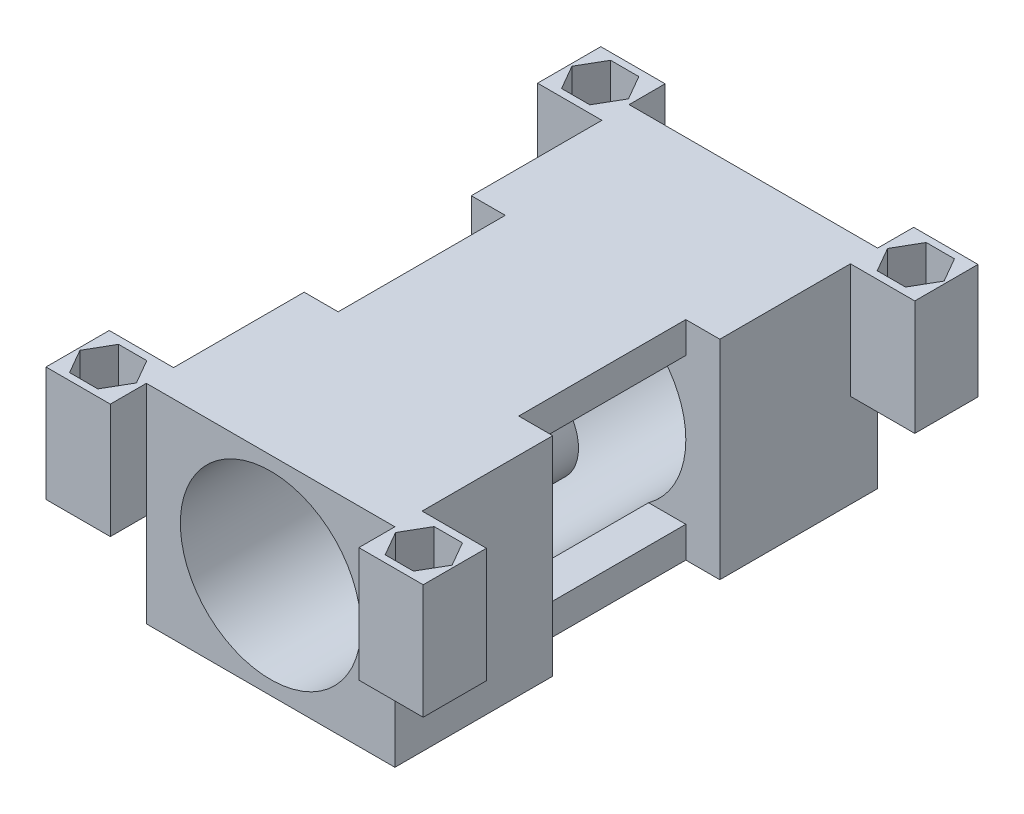
SolidWorks part; units mm, degrees
ref_plane "Front Plane" through (0, 0, 0) normal (0, 0, 1) x (1, 0, 0)
ref_plane "Top Plane" through (0, 0, 0) normal (0, 1, 0) x (1, 0, 0)
ref_plane "Right Plane" through (0, 0, 0) normal (1, 0, 0) x (0, 0, -1)
sketch "Sketch1" plane through (0, 0, 0) normal (0, 0, 1) x (1, 0, 0)
  line L0 (17, -14.25) -> (-17, -14.25)
  line L1 (-17, 14.25) -> (17, 14.25)
  line L2 (-17, 14.25) -> (-17, -14.25)
  line L3 (-17, 0) -> (17, 0) construction
  line L4 (17, 14.25) -> (17, -14.25)
  line L5 (0, 14.25) -> (0, -14.25) construction
  dimension "D2" = 34
  dimension "D3" = 28.5
extrude "Boss-Extrude1" add sketch "Sketch1" along normal blind 66.04
sketch "Sketch3" plane through (0, 0, 66.04) normal (0, 0, 1) x (1, 0, 0)
  circle A0 centre (0, 0) radius 12.35
  dimension "D1" = 24.7
extrude "Cut-Extrude1" cut sketch "Sketch3" against normal through all
sketch "Sketch7" plane through (0, 0, 66.04) normal (0, 0, 1) x (1, 0, 0)
  line L0 (0, 15.1888) -> (0, -15.3037) construction
  line L1 (-17, 14.25) -> (-25.8, 14.25)
  line L2 (-17, 14.25) -> (-17, -1.45)
  line L3 (-17, -1.45) -> (-25.8, -1.45)
  line L4 (-25.8, 14.25) -> (-25.8, -1.45)
  line L5 (17, 14.25) -> (25.8, 14.25)
  line L6 (17, 14.25) -> (17, -1.45)
  line L7 (17, -1.45) -> (25.8, -1.45)
  line L8 (25.8, 14.25) -> (25.8, -1.45)
  line L9 (-17, -14.25) -> (17, -14.25) construction
  dimension "D1" = 12.8
  dimension "D2" = 8.8
extrude "Boss-Extrude2" add sketch "Sketch7" against normal blind 3.72 and the other way blind 4.93
sketch "Sketch10" plane through (0, 0, 0) normal (0, 0, 1) x (1, 0, 0)
  line L0 (0, 15.1888) -> (0, -15.3037) construction
  line L1 (-17, 14.25) -> (-25.8, 14.25)
  line L2 (-17, 14.25) -> (-17, -1.45)
  line L3 (-17, -1.45) -> (-25.8, -1.45)
  line L4 (-25.8, 14.25) -> (-25.8, -1.45)
  line L5 (17, 14.25) -> (25.8, 14.25)
  line L6 (17, 14.25) -> (17, -1.45)
  line L7 (17, -1.45) -> (25.8, -1.45)
  line L8 (25.8, 14.25) -> (25.8, -1.45)
  line L9 (17, -14.25) -> (17, 14.25) construction
  line L10 (17, 14.25) -> (-17, 14.25) construction
  line L11 (-17, 14.25) -> (-17, -14.25) construction
  dimension "D1" = 15.7
  dimension "D2" = 8.8
extrude "Boss-Extrude3" add sketch "Sketch10" along normal blind 3.72 and the other way blind 4.93
sketch "Sketch8" plane through (0, 14.25, 0) normal (0, 1, 0) x (1, 0, 0)
  line L0 (-38.4467, -66.675) -> (30.374, -66.675) construction
  line L2 (-28.7589, -33.02) -> (31.1803, -33.02) construction
  line L3 (0, 4.5692) -> (0, -33.8299) construction
  line L4 (-17, -62.32) -> (-17, -3.72) construction
  line L6 (-25.4582, 0.635) -> (-23.5241, -2.715)
  line L7 (-17.7218, -66.675) -> (-19.6559, -63.325)
  line L8 (-19.6559, -63.325) -> (-23.5241, -63.325)
  line L9 (-23.5241, -63.325) -> (-25.4582, -66.675)
  line L10 (-25.4582, -66.675) -> (-23.5241, -70.025)
  line L11 (-23.5241, -70.025) -> (-19.6559, -70.025)
  line L12 (-19.6559, -70.025) -> (-17.7218, -66.675)
  line L13 (17.7218, -66.675) -> (19.6559, -70.025)
  line L14 (19.6559, -70.025) -> (23.5241, -70.025)
  line L15 (23.5241, -70.025) -> (25.4582, -66.675)
  line L16 (25.4582, -66.675) -> (23.5241, -63.325)
  line L17 (23.5241, -63.325) -> (19.6559, -63.325)
  line L18 (19.6559, -63.325) -> (17.7218, -66.675)
  line L19 (-23.5241, -2.715) -> (-19.6559, -2.715)
  line L20 (-19.6559, -2.715) -> (-17.7218, 0.635)
  line L21 (-17.7218, 0.635) -> (-19.6559, 3.985)
  line L22 (-19.6559, 3.985) -> (-23.5241, 3.985)
  line L23 (-23.5241, 3.985) -> (-25.4582, 0.635)
  line L24 (25.4582, 0.635) -> (23.5241, 3.985)
  line L25 (23.5241, 3.985) -> (19.6559, 3.985)
  line L26 (19.6559, 3.985) -> (17.7218, 0.635)
  line L27 (17.7218, 0.635) -> (19.6559, -2.715)
  line L28 (19.6559, -2.715) -> (23.5241, -2.715)
  line L29 (23.5241, -2.715) -> (25.4582, 0.635)
  line L30 (17, 0) -> (-17, 0) construction
  circle A0 centre (-21.59, -66.675) radius 3.35 construction
  circle A1 centre (21.59, -66.675) radius 3.35 construction
  circle A2 centre (-21.59, 0.635) radius 3.35 construction
  circle A3 centre (21.59, 0.635) radius 3.35 construction
  point P48 (-17, -33.02)
  dimension "D1" = 6.7
  dimension "D2" = 43.18
  dimension "D3" = 67.31
  dimension "D5" = 0.635
extrude "Cut-Extrude5" cut sketch "Sketch8" against normal blind 13
ref_plane "Plane1" through (0, 0, 33.02) normal (0, 0, 1) x (1, 0, 0)
sketch "Sketch11" plane through (0, 0, 33.02) normal (0, 0, 1) x (1, 0, 0)
  line L0 (-5.08, 14.25) -> (-5.08, 5.08) construction
  line L1 (17, 14.25) -> (-17, 14.25) construction
  line L2 (-17, -14.25) -> (17, -14.25) construction
  line L3 (-5.08, -14.25) -> (5.08, -14.25) construction
  line L4 (5.08, -14.25) -> (5.08, -5.08) construction
  line L5 (5.08, 14.25) -> (-5.08, 14.25) construction
  line L6 (-17, 5.08) -> (-5.08, 5.08) construction
  line L7 (-17, 14.25) -> (-17, -1.45) construction
  line L8 (17, 14.25) -> (17, -1.45) construction
  line L9 (17, 5.08) -> (17, -5.08) construction
  line L10 (17, -14.25) -> (17, -1.45) construction
  line L11 (17, -5.08) -> (5.08, -5.08) construction
  line L12 (-17, -1.45) -> (-17, -14.25) construction
  line L13 (-17, -5.08) -> (-17, 5.08) construction
  line L14 (5.08, 5.08) -> (17, 5.08) construction
  line L15 (-5.08, -5.08) -> (-5.08, -14.25) construction
  line L16 (-5.08, -5.08) -> (-17, -5.08) construction
  line L17 (5.08, 5.08) -> (5.08, 14.25) construction
  line L18 (0, 14.25) -> (0, -14.25) construction
  line L19 (17, 0) -> (-17, 0) construction
  line L20 (-5.08, 14.25) -> (-5.08, 5.08) construction
  line L21 (-5.08, -14.25) -> (5.08, -14.25) construction
  line L22 (5.08, -14.25) -> (5.08, -5.08) construction
  line L23 (5.08, 14.25) -> (-5.08, 14.25) construction
  line L24 (-17, 5.08) -> (-5.08, 5.08) construction
  line L25 (17, 5.08) -> (17, -5.08) construction
  line L26 (17, -5.08) -> (5.08, -5.08) construction
  line L27 (-17, -5.08) -> (-17, 5.08) construction
  line L28 (5.08, 5.08) -> (17, 5.08) construction
  line L29 (-5.08, -5.08) -> (-5.08, -14.25) construction
  line L30 (-5.08, -5.08) -> (-17, -5.08) construction
  line L31 (5.08, 5.08) -> (5.08, 14.25) construction
  line L32 (0, 14.25) -> (0, -14.25) construction
  line L33 (17, 0) -> (-17, 0) construction
  circle A0 centre (0, 0) radius 12.35
  dimension "D5" = 24.7
  dimension "D1" = 10.16
  dimension "D2" = 10.16
  dimension "D3" = 10.16
  dimension "D4" = 10.16
extrude "Boss-Extrude4" add sketch "Sketch11" along normal mid plane 4 separate body
sketch "Sketch13" plane through (0, 0, 33.02) normal (0, 0, 1) x (1, 0, 0)
  line L0 (17, -14.25) -> (17, 14.25)
  line L3 (-12.35, 10) -> (-7.2472, 10)
  line L4 (-3, 0) -> (-3, 11.9801)
  line L5 (-12.35, -10) -> (-7.2472, -10)
  line L6 (-3, 0) -> (-3, -11.9801)
  line L7 (12.35, 10) -> (7.2472, 10)
  line L9 (3, 0) -> (3, 11.9801)
  line L10 (17, 14.25) -> (12.35, 14.25)
  line L12 (12.35, -10) -> (7.2472, -10)
  line L13 (3, 0) -> (3, -11.9801)
  line L14 (-21.7997, 0) -> (22.981, 0) construction
  line L15 (0, 16.7794) -> (0, -17.4237) construction
  line L16 (17, 14.25) -> (-17, 14.25) construction
  line L17 (12.35, 14.25) -> (12.35, 10)
  line L18 (17, -14.25) -> (12.35, -14.25)
  line L19 (-17, -14.25) -> (17, -14.25) construction
  line L20 (12.35, -14.25) -> (12.35, -10)
  line L21 (-12.35, 10) -> (-12.35, 14.25)
  line L22 (-12.35, 14.25) -> (-17, 14.25)
  line L23 (-17, 14.25) -> (-17, -14.25)
  line L24 (-17, -14.25) -> (-12.35, -14.25)
  line L25 (-12.35, -14.25) -> (-12.35, -10)
  line L26 (12.35, 10) -> (12.35, -10) construction
  line L28 (-12.35, 10) -> (-12.35, -10) construction
  arc A0 (-1.7605, 2.4291) -> (-1.7605, -2.4291) centre (0, 0) ccw construction
  arc A1 (-7.2472, -10) -> (-3, -11.9801) centre (0, 0) ccw
  arc A2 (7.2472, 10) -> (3, 11.9801) centre (0, 0) ccw
  arc A3 (1.7605, -2.4291) -> (1.7605, 2.4291) centre (0, 0) ccw construction
  arc A4 (-7.2472, -10) -> (-3, -11.9801) centre (0, 0) ccw construction
  arc A5 (7.2472, 10) -> (3, 11.9801) centre (0, 0) ccw construction
  arc A6 (-3, 11.9801) -> (-7.2472, 10) centre (0, 0) ccw
  arc A7 (-3, 11.9801) -> (-7.2472, 10) centre (0, 0) ccw construction
  arc A8 (3, -11.9801) -> (7.2472, -10) centre (0, 0) ccw
  arc A9 (3, -11.9801) -> (7.2472, -10) centre (0, 0) ccw construction
  circle A11 centre (0, 0) radius 12.35 construction
  circle A12 centre (0, 0) radius 12.35 construction
  dimension "D1" = 6
  dimension "D3" = 24.7
  dimension "D2" = 20
extrude "Cut-Extrude7" cut sketch "Sketch13" against normal mid plane 22.86
sketch "Sketch14" plane through (0, 0, 33.02) normal (0, 0, 1) x (1, 0, 0)
  circle A0 centre (0, 0) radius 6
  dimension "D1" = 12
extrude "Boss-Extrude5" add sketch "Sketch14" along normal mid plane 6.2
sketch "Sketch15" plane through (0, 0, 36.12) normal (0, 0, 1) x (1, 0, 0)
  circle A0 centre (0, 0) radius 3.325
  dimension "D1" = 6.65
extrude "Cut-Extrude8" cut sketch "Sketch15" against normal blind 2.5
sketch "Sketch16" plane through (0, 0, 29.92) normal (0, 0, -1) x (-1, 0, 0)
  circle A0 centre (0, 0) radius 3.325
  dimension "D1" = 6.65
extrude "Cut-Extrude9" cut sketch "Sketch16" against normal blind 2.5
chamfer "Chamfer1" [suppressed] distance 0.8 distance2 0.6
extrude "Cut-Extrude11" cut sketch "Sketch18" against normal blind 50
sketch "Sketch18" plane through (132.324, 1.25, 1.7763) normal (0, 1, 0) x (1, 0, 0)
  line L1 (-149.324, -30.6137) -> (-115.324, -30.6137) construction
  line L4 (-132.324, -63.3037) -> (-132.324, 2.4063) construction
  circle A0 centre (-110.734, 3.0413) radius 1.651
  circle A1 centre (-110.734, -64.2687) radius 1.651
  circle A2 centre (-153.914, -64.2687) radius 1.651
  circle A3 centre (-153.914, 3.0413) radius 1.651
extrude "Cut-Extrude17" cut sketch "Sketch25" against normal blind 50
sketch "Sketch25" plane through (132.324, 1.25, 1.8463) normal (0, 1, 0) x (1, 0, 0)
  line L1 (-149.324, -31.1737) -> (-115.324, -31.1737) construction
  line L4 (-132.324, -65.4037) -> (-132.324, 1.8463) construction
  circle A0 centre (-110.734, 2.4813) radius 1.75
  circle A1 centre (-110.734, -64.8287) radius 1.75
  circle A2 centre (-153.914, -64.8287) radius 1.75
  circle A3 centre (-153.914, 2.4813) radius 1.75
